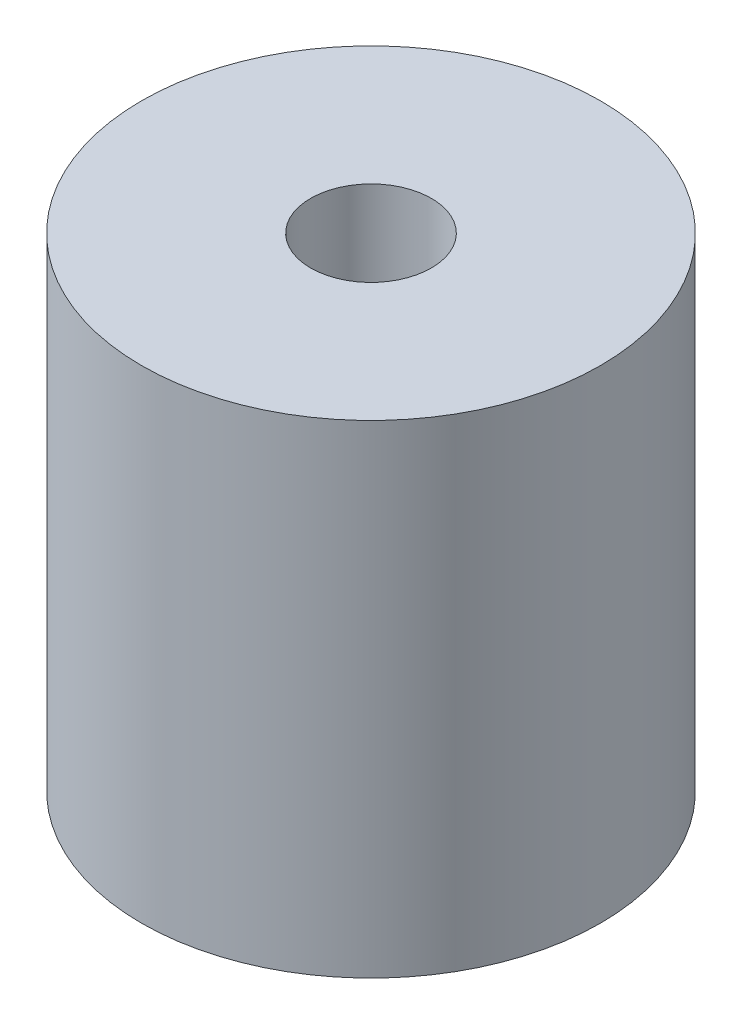
SolidWorks part; units mm, degrees
ref_plane "Front Plane" through (0, 0, 0) normal (0, 0, 1) x (1, 0, 0)
ref_plane "Top Plane" through (0, 0, 0) normal (0, 1, 0) x (1, 0, 0)
ref_plane "Right Plane" through (0, 0, 0) normal (1, 0, 0) x (0, 0, -1)
sketch "Sketch1" plane through (0, 0, 0) normal (0, 1, 0) x (1, 0, 0)
  circle A0 centre (0, 0) radius 9.5
  circle A1 centre (0, 0) radius 2.5
  dimension "D1" = 5
  dimension "D2" = 19
extrude "Boss-Extrude1" add sketch "Sketch1" along normal blind 20
